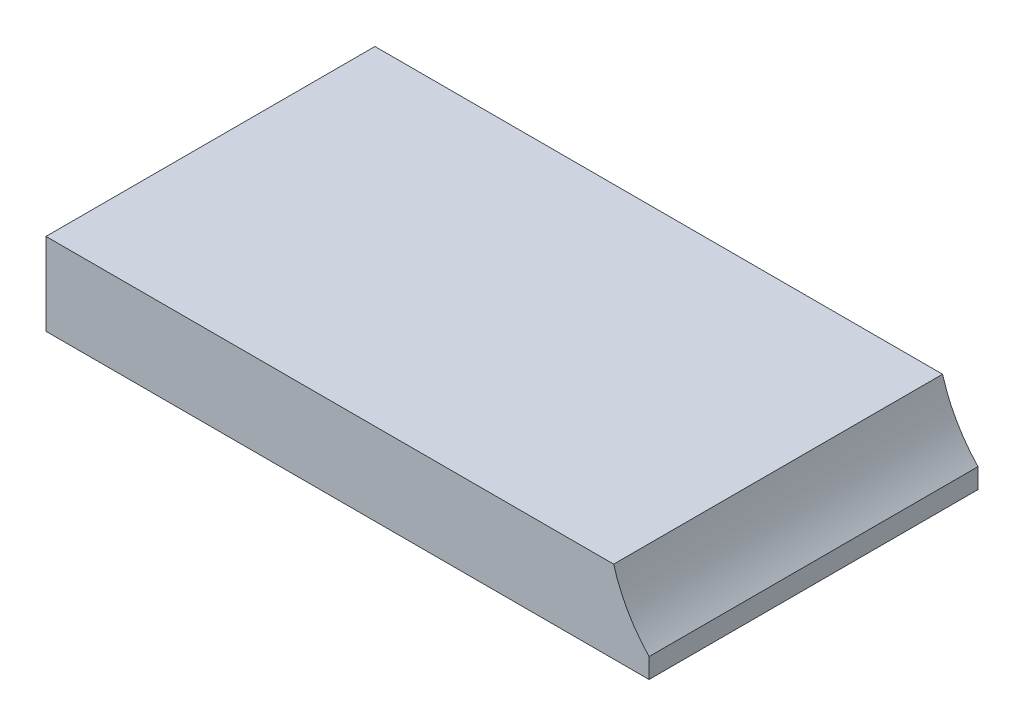
SolidWorks part; units mm, degrees
material "PA Тип 6"
ref_plane "Спереди" through (0, 0, 0) normal (0, 0, 1) x (1, 0, 0)
ref_plane "Сверху" through (0, 0, 0) normal (0, 1, 0) x (1, 0, 0)
ref_plane "Справа" through (0, 0, 0) normal (1, 0, 0) x (0, 0, -1)
sketch "Эскиз1" plane through (0, 0, 0) normal (0, 1, 0) x (1, 0, 0)
  line L1 (0, 0) -> (22, 0)
  line L2 (0, 0) -> (0, 12)
  line L3 (0, 12) -> (22, 12)
  line L4 (22, 0) -> (22, 12)
  dimension "D1" = 22
  dimension "D2" = 12
extrude "Бобышка-Вытянуть1" add sketch "Эскиз1" along normal blind 3
sketch "Эскиз2" plane through (0, 0, 0) normal (0, 0, 1) x (1, 0, 0)
  line L0 (22, 3) -> (22, 0) construction
  line L1 (0, 3) -> (22, 3) construction
  circle A0 centre (26, 4.5) radius 5.5
  dimension "D1" = 11
  dimension "D2" = 4
  dimension "D3" = 1.5
extrude "Вырез-Вытянуть1" cut sketch "Эскиз2" against normal through all
